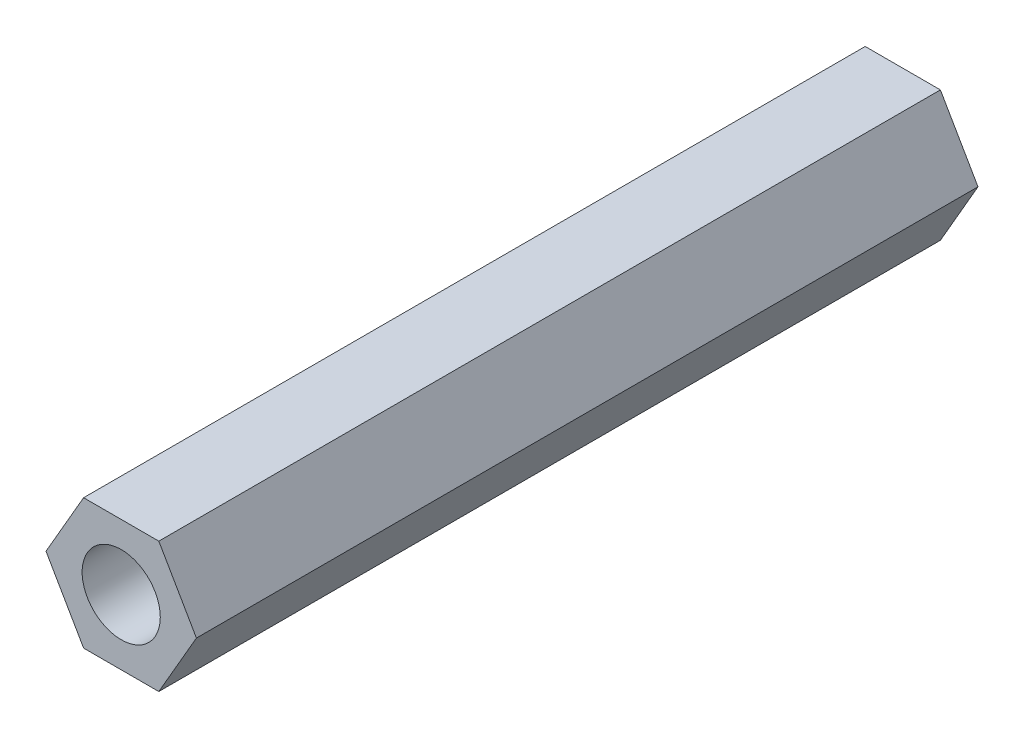
SolidWorks part; units mm, degrees
material "AISI 304"
ref_plane "前视基准面" through (0, 0, 0) normal (0, 0, 1) x (1, 0, 0)
ref_plane "上视基准面" through (0, 0, 0) normal (0, 1, 0) x (1, 0, 0)
ref_plane "右视基准面" through (0, 0, 0) normal (1, 0, 0) x (0, 0, -1)
sketch "草图1" plane through (0, 0, 0) normal (0, 0, 1) x (1, 0, 0)
  line L1 (1.4434, -2.5) -> (2.8868, 0)
  line L2 (2.8868, 0) -> (1.4434, 2.5)
  line L3 (1.4434, 2.5) -> (-1.4434, 2.5)
  line L4 (-1.4434, 2.5) -> (-2.8868, 0)
  line L5 (-2.8868, 0) -> (-1.4434, -2.5)
  line L6 (-1.4434, -2.5) -> (1.4434, -2.5)
  circle A0 centre (0, 0) radius 1.5
  circle A1 centre (0, 0) radius 2.5 construction
  dimension "D1" = 3
  dimension "D2" = 5
extrude "凸台-拉伸1" add sketch "草图1" along normal blind 30
